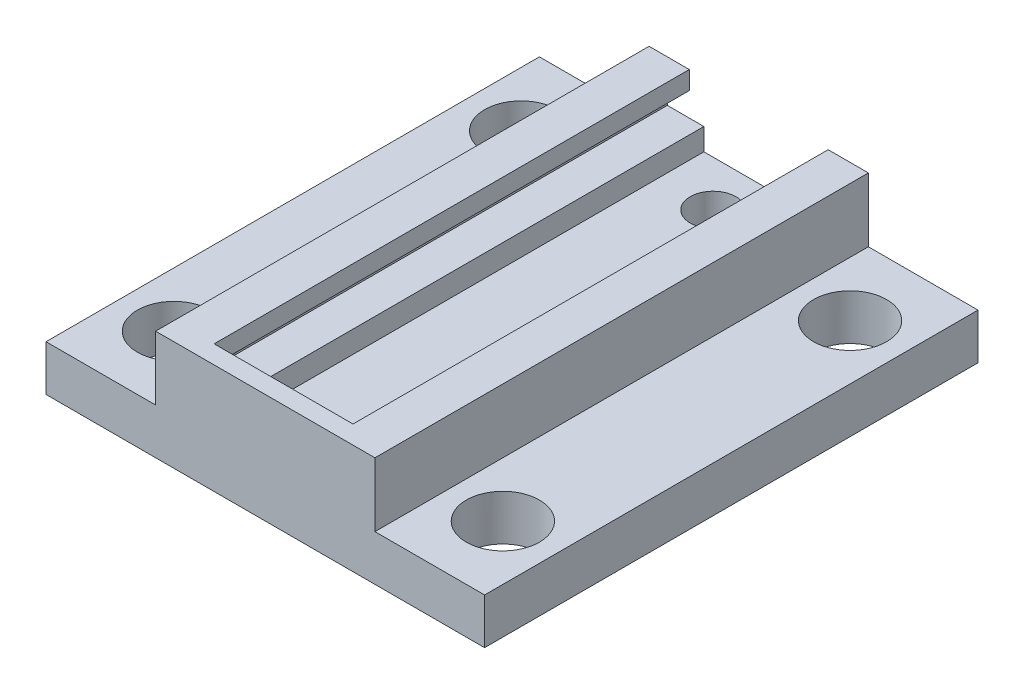
SolidWorks part; units mm, degrees
ref_plane "Front Plane" through (0, 0, 0) normal (0, 0, 1) x (1, 0, 0)
ref_plane "Top Plane" through (0, 0, 0) normal (0, 1, 0) x (1, 0, 0)
ref_plane "Right Plane" through (0, 0, 0) normal (1, 0, 0) x (0, 0, -1)
sketch "Sketch1" plane through (0, 0, 0) normal (0, 0, 1) x (1, 0, 0)
  line L0 (3.81, -3.1911) -> (-3.81, -3.1911)
  line L1 (-3.81, -3.1911) -> (-3.81, -1.6671)
  line L2 (-3.81, -1.6671) -> (-6.35, -1.6671)
  line L3 (-6.35, -1.6671) -> (-6.35, -0.0161)
  line L4 (-6.35, -0.0161) -> (-4.826, -0.0161)
  line L5 (-4.826, -0.0161) -> (-4.826, 1.2539)
  line L6 (-4.826, 1.2539) -> (-7.62, 1.2539)
  line L7 (-7.62, 1.2539) -> (-7.62, -3.1911)
  line L8 (-8.89, -6.3661) -> (8.89, -6.3661)
  line L10 (7.62, 1.2539) -> (7.62, -3.1911)
  line L11 (4.826, 1.2539) -> (7.62, 1.2539)
  line L12 (4.826, -0.0161) -> (4.826, 1.2539)
  line L13 (6.35, -0.0161) -> (4.826, -0.0161)
  line L14 (6.35, -1.6671) -> (6.35, -0.0161)
  line L15 (3.81, -1.6671) -> (6.35, -1.6671)
  line L16 (3.81, -3.1911) -> (3.81, -1.6671)
  line L17 (-7.62, -3.1911) -> (-15.24, -3.1911)
  line L18 (-15.24, -3.1911) -> (-15.24, -6.3661)
  line L19 (-15.24, -6.3661) -> (-8.89, -6.3661)
  line L20 (0, -6.3661) -> (0, -10.8695) construction
  line L21 (15.24, -6.3661) -> (8.89, -6.3661)
  line L22 (15.24, -3.1911) -> (15.24, -6.3661)
  line L23 (7.62, -3.1911) -> (15.24, -3.1911)
  dimension "D1" = 1.27
  dimension "D2" = 3.175
  dimension "D3" = 2.54
  dimension "D4" = 1.524
  dimension "D5" = 7.62
  dimension "D6" = 1.524
  dimension "D7" = 1.27
  dimension "D8" = 1.651
extrude "Boss-Extrude1" add sketch "Sketch1" along normal blind 34.29
sketch "Sketch3" plane through (0, 0, 34.29) normal (0, 0, 1) x (1, 0, 0)
  line L1 (-7.62, 1.2539) -> (7.62, 1.2539)
  line L2 (-7.62, 1.2539) -> (-7.62, -3.1911)
  line L3 (-7.62, -3.1911) -> (7.62, -3.1911)
  line L4 (7.62, 1.2539) -> (7.62, -3.1911)
extrude "Boss-Extrude3" add sketch "Sketch3" against normal blind 1.27
sketch "Sketch4" plane through (0, 0, 0) normal (0, 1, 0) x (1, 0, 0)
  line L0 (0, 0) -> (0, -27.557) construction
  line L1 (-15.24, -34.29) -> (-15.24, 0) construction
  line L2 (-7.62, 0) -> (-15.24, 0) construction
  line L3 (-7.62, -34.29) -> (-15.24, -34.29) construction
  circle A0 centre (-11.43, -5.08) radius 2.54
  circle A1 centre (-11.43, -29.21) radius 2.54
  circle A2 centre (11.43, -29.21) radius 2.54
  circle A3 centre (11.43, -5.08) radius 2.54
  dimension "D1" = 5.08
  dimension "D2" = 5.08
  dimension "D3" = 3.81
  dimension "D4" = 3.81
  dimension "D5" = 5.08
  dimension "D6" = 5.08
extrude "Cut-Extrude1" cut sketch "Sketch4" against normal through all
sketch "Sketch5" plane through (0, -3.1911, 0) normal (0, 1, 0) x (1, 0, 0)
  line L0 (3.81, 0) -> (-3.81, 0) construction
  circle A0 centre (0, -3.175) radius 1.5875
  dimension "D1" = 3.175
  dimension "D2" = 3.175
extrude "Cut-Extrude2" cut sketch "Sketch5" against normal through all
